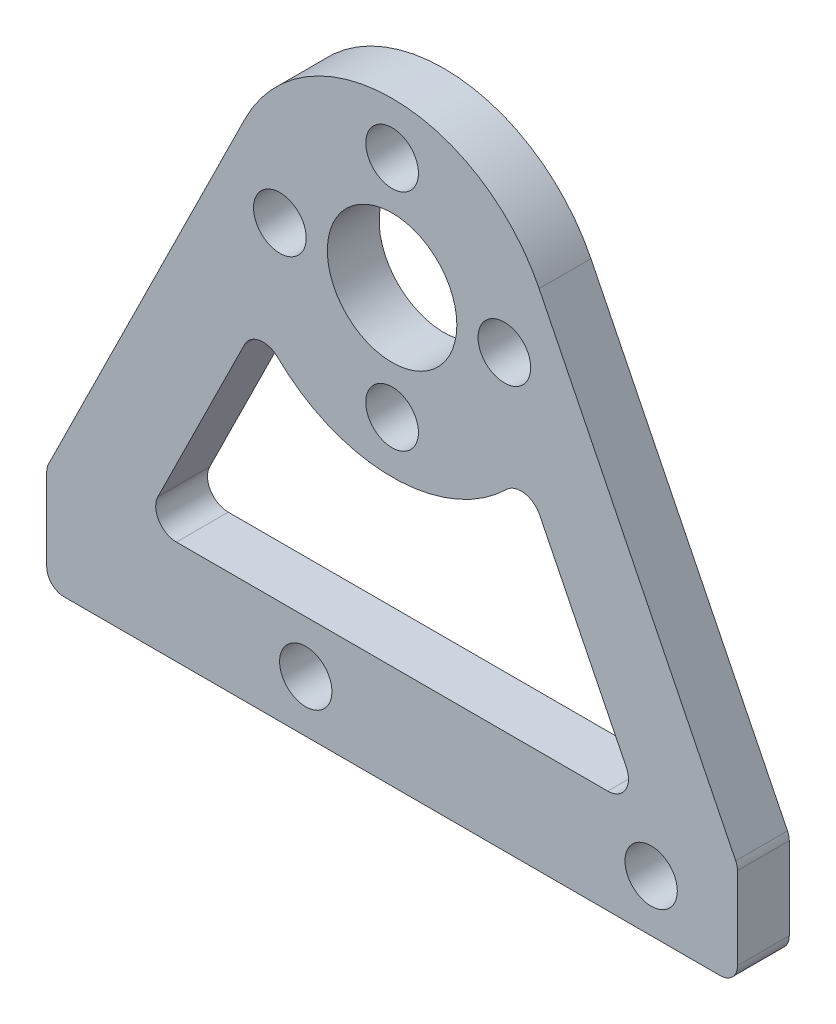
SolidWorks part; units mm, degrees
material "Thornel Mat VMA"
ref_plane "前视基准面" through (0, 0, 0) normal (0, 0, 1) x (1, 0, 0)
ref_plane "上视基准面" through (0, 0, 0) normal (0, 1, 0) x (1, 0, 0)
ref_plane "右视基准面" through (0, 0, 0) normal (1, 0, 0) x (0, 0, -1)
sketch "草图1" plane through (0, 0, 0) normal (0, 0, 1) x (1, 0, 0)
  line L0 (0, 0) -> (0, -25) construction
  line L1 (-20, -25) -> (20, -25)
  line L2 (20, -25) -> (20, -19)
  line L3 (20, -19) -> (8.5148, 4.2129)
  line L4 (-20, -19) -> (-8.5148, 4.2129)
  line L5 (-20, -25) -> (-20, -19)
  circle A0 centre (0, 0) radius 6.5 construction
  circle A1 centre (0, 6.5) radius 1.525
  circle A2 centre (6.5, 0) radius 1.525
  circle A3 centre (0, -6.5) radius 1.525
  circle A4 centre (-6.5, 0) radius 1.525
  circle A5 centre (0, 0) radius 3.75
  arc A6 (8.5148, 4.2129) -> (-8.5148, 4.2129) centre (0, 0) ccw
  point P14 (0, 0)
  point P18 (0, -25)
  dimension "D1" = 13
  dimension "D2" = 3.05
  dimension "D4" = 7.5
  dimension "D5" = 3
  dimension "D6" = 25
  dimension "D7" = 40
  dimension "D8" = 6
  dimension "D3" = 4
extrude "凸台-拉伸1" add sketch "草图1" along normal blind 3
fillet "圆角1" radius 1 4 edges at (-20, -25, 1.5) (-20, -19, 1.5) (20, -19, 1.5) (20, -25, 1.5)
sketch "草图2" plane through (0, 0, 0) normal (0, 0, -1) x (-1, 0, 0)
  circle A0 centre (5, -22) radius 1.25 construction
  circle A1 centre (-15, -22) radius 1.25 construction
  circle A2 centre (5, -22) radius 1.25 construction
  circle A3 centre (-15, -22) radius 1.25 construction
  circle A4 centre (-15, -22) radius 1.515
  circle A5 centre (5, -22) radius 1.515
  dimension "D1" = 3.03
extrude "切除-拉伸1" cut sketch "草图2" against normal blind 10
sketch "草图3" plane through (0, 0, 0) normal (0, 0, -1) x (-1, 0, 0)
  line L0 (-7.7436, -5.5033) -> (-14.4215, -19)
  line L1 (-14.4215, -19) -> (14.4215, -19)
  line L2 (14.4215, -19) -> (7.7436, -5.5033)
  line L3 (8.5148, 4.2129) -> (19.8963, -18.7904) construction
  line L4 (-19.8963, -18.7904) -> (-8.5148, 4.2129) construction
  arc A0 (-7.7436, -5.5033) -> (7.7436, -5.5033) centre (0, 0) ccw
  circle A1 centre (-15, -22) radius 1.515 construction
  dimension "D1" = 19
  dimension "D2" = 3
  dimension "D3" = 5
  dimension "D4" = 5
extrude "切除-拉伸2" cut sketch "草图3" against normal blind 10
fillet "圆角2" radius 1.2 4 edges at (-7.7436, -5.5033, 1.5) (7.7436, -5.5033, 1.5) (-14.4215, -19, 1.5) (14.4215, -19, 1.5)
equation "\"D4@草图3\"=\"D3@草图3\""
